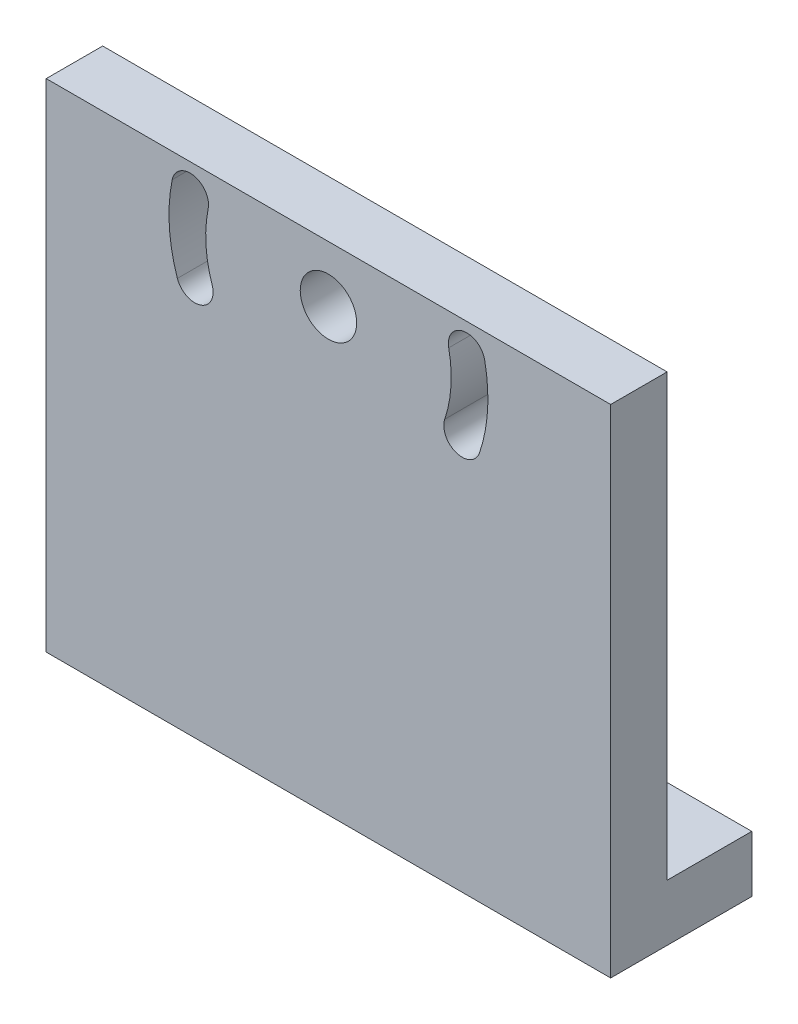
SolidWorks part; units mm, degrees
ref_plane "前视基准面" through (0, 0, 0) normal (0, 0, 1) x (1, 0, 0)
ref_plane "上视基准面" through (0, 0, 0) normal (0, 1, 0) x (1, 0, 0)
ref_plane "右视基准面" through (0, 0, 0) normal (1, 0, 0) x (0, 0, -1)
sketch "草图1" plane through (0, 0, 0) normal (0, 0, 1) x (1, 0, 0)
  line L0 (150, 103.55) -> (0, 90.4267)
  line L1 (0, 0) -> (150, 0)
  line L2 (0, 0) -> (0, 90.4267)
  line L4 (150, 0) -> (150, 103.55)
  dimension "D1" = 103.55
extrude "凸台-拉伸1" add sketch "草图1" along normal blind 10
sketch "草图2" plane through (0, 0, 0) normal (0, 0, -1) x (-1, 0, 0)
  line L1 (0, 90.4267) -> (-169.8821, 90.4267)
  line L2 (0, 90.4267) -> (0, 115.524)
  line L3 (0, 115.524) -> (-169.8821, 115.524)
  line L4 (-169.8821, 90.4267) -> (-169.8821, 115.524)
extrude "切除-拉伸1" cut sketch "草图2" against normal through all
sketch "草图4" plane through (0, 0, 10) normal (0, 0, 1) x (1, 0, 0)
  line L1 (150, 0) -> (0, 0)
  line L2 (150, 0) -> (150, 103)
  line L3 (150, 103) -> (0, 103)
  line L4 (0, 0) -> (0, 103)
  dimension "D1" = 103
extrude "凸台-拉伸2" add sketch "草图4" against normal up to surface (10 mm away) up to face at (75, 45.2134, 0)
sketch "草图5" plane through (0, 0, 10) normal (0, 0, 1) x (1, 0, 0)
  line L0 (0, 0) -> (150, 0) construction
  line L1 (150, 103) -> (100, 103)
  line L2 (150, 103) -> (150, 0)
  line L3 (150, 0) -> (100, 0)
  line L4 (100, 103) -> (100, 0)
  dimension "D1" = 50
extrude "切除-拉伸2" cut sketch "草图5" against normal through all
sketch "草图7" plane through (0, 0, 10) normal (0, 0, 1) x (1, 0, 0)
  line L1 (0, 103) -> (130.9494, 103)
  line L2 (0, 103) -> (0, 43)
  line L3 (0, 43) -> (130.9494, 43)
  line L4 (130.9494, 103) -> (130.9494, 43)
  dimension "D1" = 60
extrude "切除-拉伸3" cut sketch "草图7" against normal blind 10
sketch "草图8" plane through (0, 0, 0) normal (0, 0, -1) x (-1, 0, 0)
  line L0 (-50, 43) -> (-50, 0) construction
  line L1 (0, 43) -> (-100, 43) construction
  line L2 (0, 0) -> (-100, 0) construction
  circle A0 centre (-50, 33) radius 5
  dimension "D1" = 10
  dimension "D2" = 10
extrude "切除-拉伸4" cut sketch "草图8" against normal through all
sketch "草图11" plane through (0, 0, 0) normal (0, 0, -1) x (-1, 0, 0)
  line L0 (0, 43) -> (-100, 43) construction
  arc A0 (-76.7645, 23.96) -> (-70.6063, 26.04) centre (-73.6854, 25) ccw
  circle A1 centre (-50, 33) radius 5 construction
  circle A2 centre (-50, 33) radius 25 construction
  arc A3 (-71.3106, 37.35) -> (-77.6792, 38.65) centre (-74.4949, 38) ccw
  arc A4 (-77.6792, 38.65) -> (-76.7645, 23.96) centre (-50, 33) ccw
  arc A5 (-71.3106, 37.35) -> (-70.6063, 26.04) centre (-50, 33) ccw
  dimension "D1" = 6.5
  dimension "D3" = 50
  dimension "D4" = 6.5
  dimension "D2" = 25
  dimension "D5" = 5
  dimension "D6" = 18
extrude "切除-拉伸5" cut sketch "草图11" against normal through all
ref_plane "基准面1" through (50, 0, 0) normal (-1, 0, 0) x (0, 0, 1)
mirror "镜向1" about plane through (50, 0, 0) normal (-1, 0, 0) of "切除-拉伸5"
sketch "草图12" plane through (0, 0, 0) normal (0, -1, 0) x (1, 0, 0)
  line L1 (100, 0) -> (0, 0)
  line L2 (100, 0) -> (100, 10)
  line L3 (100, 10) -> (0, 10)
  line L4 (0, 0) -> (0, 10)
extrude "凸台-拉伸3" add sketch "草图12" along normal blind 45
sketch "草图13" plane through (0, 0, 10) normal (0, 0, 1) x (1, 0, 0)
  line L0 (100, 43) -> (100, -45) construction
  line L1 (0, -45) -> (100, -45)
  line L2 (0, -45) -> (0, -40)
  line L3 (0, -40) -> (100, -40)
  line L4 (100, -45) -> (100, -40)
  dimension "D1" = 5
extrude "凸台-拉伸4" add sketch "草图13" against normal blind 25
sketch "草图14" plane through (0, -40, 0) normal (0, 1, 0) x (1, 0, 0)
  line L1 (100, 15) -> (0, 15)
  line L2 (100, 15) -> (100, 0)
  line L3 (100, 0) -> (0, 0)
  line L4 (0, 15) -> (0, 0)
extrude "凸台-拉伸5" add sketch "草图14" along normal blind 5
sketch "草图15" plane through (0, -35, 0) normal (0, 1, 0) x (1, 0, 0)
  line L0 (50, 0) -> (50, 15) construction
  line L1 (0, 0) -> (100, 0) construction
  line L2 (100, 15) -> (0, 15) construction
  circle A0 centre (82.5, 6.8853) radius 2.75
  circle A1 centre (17.5, 6.8853) radius 2.75
  dimension "D1" = 5.5
  dimension "D2" = 65
extrude "切除-拉伸6" cut sketch "草图15" against normal through all
